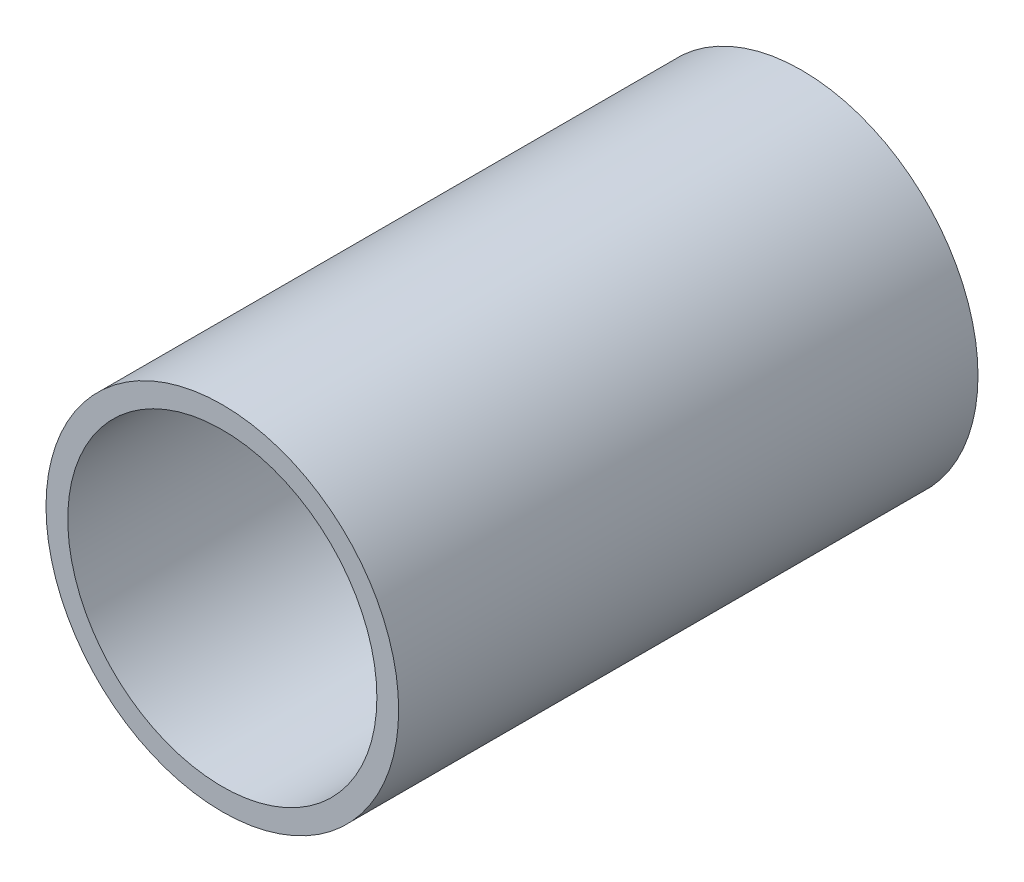
SolidWorks part; units mm, degrees
material "PVC Rigid"
ref_plane "Front Plane" through (0, 0, 0) normal (0, 0, 1) x (1, 0, 0)
ref_plane "Top Plane" through (0, 0, 0) normal (0, 1, 0) x (1, 0, 0)
ref_plane "Right Plane" through (0, 0, 0) normal (1, 0, 0) x (0, 0, -1)
sketch "Sketch1" plane through (0, 0, 0) normal (0, 0, 1) x (1, 0, 0)
  circle A0 centre (0, 0) radius 44.45
  dimension "Pipe OD" = 88.9
extrude "Extrude-Thin1" add sketch "Sketch1" along normal mid plane 146.05 thin thin type one direction reverse wall 5.4864
